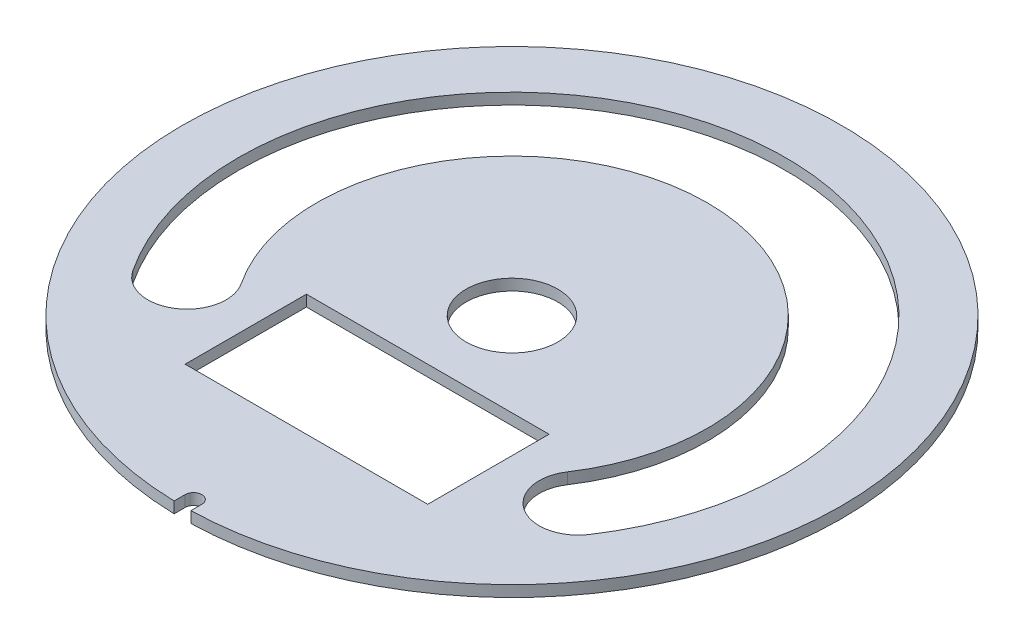
SolidWorks part; units mm, degrees
material "AISI 304"
ref_plane "Front Plane" through (0, 0, 0) normal (0, 0, 1) x (1, 0, 0)
ref_plane "Top Plane" through (0, 0, 0) normal (0, 1, 0) x (1, 0, 0)
ref_plane "Right Plane" through (0, 0, 0) normal (1, 0, 0) x (0, 0, -1)
sketch "Эскиз1" plane through (0, 0, 0) normal (0, 1, 0) x (1, 0, 0)
  line L0 (0, -12.9575) -> (0, -29.4825) construction
  line L1 (-10.85, -18.3825) -> (10.85, -18.3825)
  line L2 (-10.85, -18.3825) -> (-10.85, -7.5325)
  line L3 (-10.85, -7.5325) -> (10.85, -7.5325)
  line L4 (10.85, -18.3825) -> (10.85, -7.5325)
  line L5 (-10.85, -18.3825) -> (10.85, -7.5325) construction
  line L6 (-10.85, -7.5325) -> (10.85, -18.3825) construction
  line L7 (-17.5, -11.5629) -> (17.5, -11.5629) construction
  line L8 (0, -28.4825) -> (0, -30.7667) construction
  line L9 (0.75, -28.5037) -> (0.75, -29.4655)
  line L10 (-0.75, -28.5037) -> (-0.75, -29.4655)
  line L11 (-0.75, -28.5037) -> (0.75, -28.5037) construction
  arc A0 (0.75, -29.4655) -> (-0.75, -29.4655) centre (0, 0) ccw
  circle A1 centre (0, 0) radius 4.1
  arc A2 (-17.5, -11.5629) -> (17.5, -11.5629) centre (0, 0) cw construction
  arc A3 (20.4201, -13.4923) -> (-20.4201, -13.4923) centre (0, 0) ccw
  arc A4 (14.5799, -9.6335) -> (-14.5799, -9.6335) centre (0, 0) ccw
  arc A5 (14.5799, -9.6335) -> (20.4201, -13.4923) centre (17.5, -11.5629) ccw
  arc A6 (-20.4201, -13.4923) -> (-14.5799, -9.6335) centre (-17.5, -11.5629) ccw
  arc A7 (0.75, -28.5037) -> (-0.75, -28.5037) centre (0, -28.4825) ccw
  arc A9 (0.75, -29.4655) -> (-0.75, -29.4655) centre (0, -12.9575) cw construction
  point P4 (0, -12.9575)
  point P13 (0, 20.975)
  point P22 (0, -29.6208)
  dimension "D1" = 58.95
  dimension "D2" = 8.2
  dimension "D6" = 3.5
  dimension "D7" = 5
  dimension "D11" = 0.7503
  dimension "D3" = 21.7
  dimension "D4" = 10.85
  dimension "D5" = 11.1
  dimension "D8" = 35
  dimension "D9" = 1.5
  dimension "D10" = 1
extrude "Бобышка-Вытянуть1" add sketch "Эскиз1" along normal blind 1
